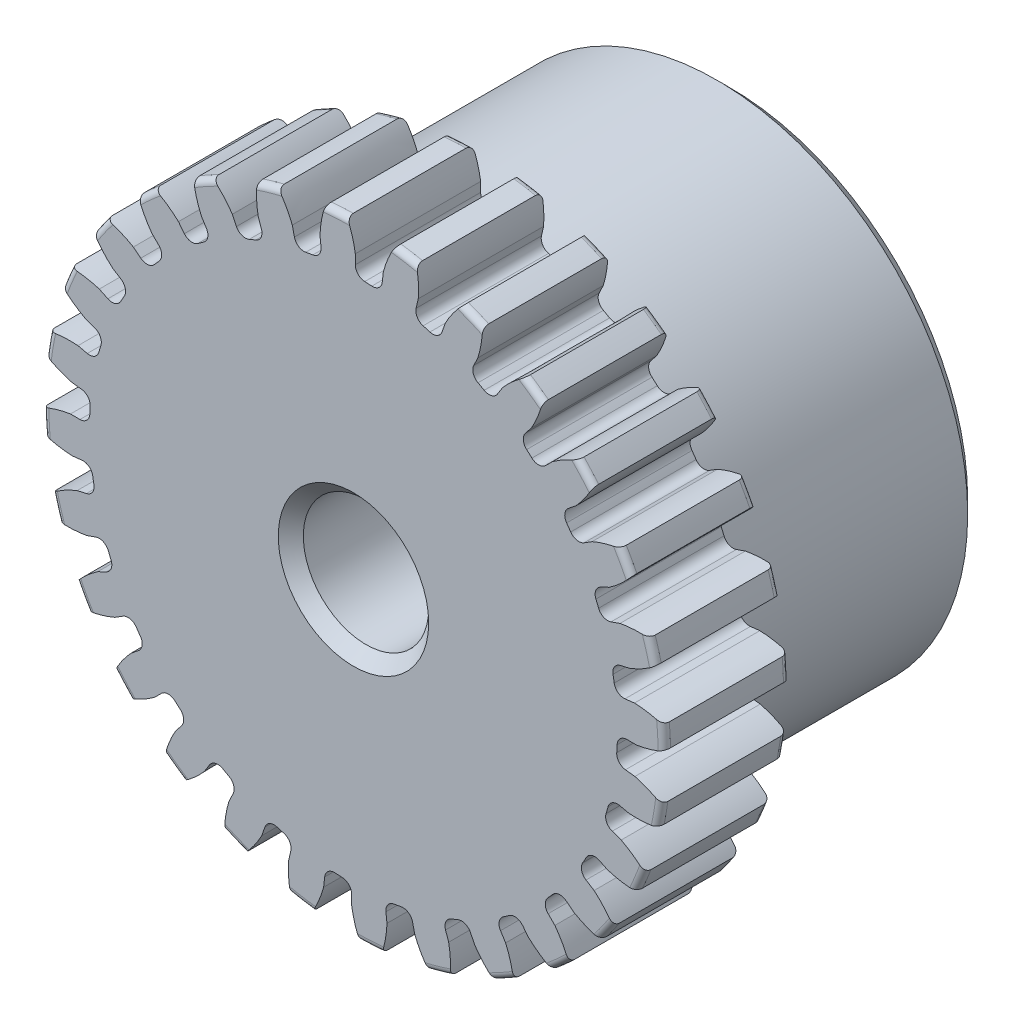
SolidWorks part; units mm, degrees
ref_plane "Front" through (0, 0, 0) normal (0, 0, 1) x (1, 0, 0)
ref_plane "Top" through (0, 0, 0) normal (0, 1, 0) x (1, 0, 0)
ref_plane "Right" through (0, 0, 0) normal (1, 0, 0) x (0, 0, -1)
sketch "Sketch1" plane through (0, 0, 0) normal (0, 0, 1) x (1, 0, 0)
  line L0 (-355.6, 0) -> (355.6, 0) construction
  circle A0 centre (0, 0) radius 7.874
  circle A1 centre (0, 0) radius 7.4041 construction
  circle A3 centre (0, 0) radius 6.6841 construction
  dimension "D1" = 1.1899
  dimension "OD" = 15.748
  dimension "Ptich Dia" = 14.8082
  dimension "Root Dia" = 13.3681
  dimension "D3" = 0.4699
  dimension "Number of Teeth" = 711.2
extrude "Boss-Extrude1" add sketch "Sketch1" against normal blind 3.175
sketch "Sketch2" plane through (0, 0, 0) normal (1, 0, 0) x (0, 0, -1)
  line L0 (3.175, 0) -> (9.525, 0)
  line L1 (3.175, 0) -> (3.175, 6.35)
  line L2 (3.175, 6.35) -> (9.525, 6.35)
  line L3 (9.525, 6.35) -> (9.525, 0)
  point P5 (9.525, -6.35)
  point P6 (0, -7.874)
  point P7 (3.175, -7.874)
  point P9 (0, 7.874)
  dimension "Face Wd" = 3.175
  dimension "B Hub Dia" = 12.7
  dimension "D O'all Lg." = 9.525
revolve "Revolve1" add sketch "Sketch2" angle 360 about L0
fillet "Fillet2" radius 0.1575 3 edges at (7.874, 0, -3.175) (7.874, 0, 0) (6.35, 0, -3.175)
sketch "Sketch3" plane through (0, 0, 0) normal (0, 0, 1) x (1, 0, 0)
  line L0 (0, 0) -> (0, 7.874) construction
  line L1 (-1.7948, 6.9399) -> (0, 7.4041)
  line L2 (-9.5921, 7.4041) -> (9.5921, 7.4041) construction
  line L3 (-9.2865, 5.0024) -> (9.2865, 9.8058) construction
  line L4 (-1.7948, 6.9399) -> (0, 0) construction
  line L5 (-4.5779, 5.516) -> (0, 0) construction
  line L6 (-4.5779, 5.516) -> (-0.7458, 8.6964) construction
  line L7 (-1.2515, 7.0582) -> (0, 0) construction
  line L8 (-1.2515, 7.0582) -> (0.0263, 7.2847) construction
  arc A0 (-1.7948, 6.9399) -> (-4.5779, 5.516) centre (0, 0) ccw
  circle A1 centre (0, 0) radius 7.4041 construction
  circle A2 centre (0, 0) radius 7.1683 construction
  arc A3 (-1.7948, 6.9399) -> (-1.2515, 7.0582) centre (0, 0) cw
  circle A4 centre (0, 0) radius 7.874 construction
  point P6 (0, 7.4041)
  dimension "D1" = 1.8538
  dimension "Pressure Angle" = 14.5
  dimension "D2" = 3.1515
  dimension "D3" = 4.98
  dimension "D4" = 0.5562
  dimension "D5" = 1.2977
sketch "Sketch4" plane through (0, 0, 0) normal (0, 0, 1) x (1, 0, 0)
  line L0 (0, 0) -> (0.4145, 7.3808) construction
  line L1 (0.0464, 7.1681) -> (0.0464, 6.6839)
  line L2 (0, 7.4041) -> (0.829, 7.3575) construction
  line L3 (0.7565, 7.1282) -> (0.7022, 6.6471)
  line L4 (0.0464, 6.6839) -> (0, 0) construction
  line L5 (0, 0) -> (0, 7.874) construction
  line L6 (-4.5779, 5.516) -> (-0.7458, 8.6964) construction
  line L7 (-4.5779, 5.516) -> (-0.7458, 8.6964) construction
  arc A0 (0.7022, 6.6471) -> (0.0464, 6.6839) centre (0, 0) ccw
  arc A1 (0, 7.4041) -> (0.829, 7.3575) centre (0, 0) cw construction
  circle A2 centre (0, 0) radius 7.4041 construction
  circle A3 centre (0, 0) radius 7.1683 construction
  circle A4 centre (0, 0) radius 6.6841 construction
  arc A5 (1.7148, 8.5582) -> (-0.7458, 8.6964) centre (0, 0) ccw
  spline S0 degree 2 poles (-0.7458, 8.6964) (-0.0823, 8.0256) (0.0464, 7.1681) knots 0 0 0 1 1 1
  spline S1 degree 2 poles (1.7148, 8.5582) (0.9804, 7.9659) (0.7565, 7.1282) knots 0 0 0 1 1 1
  dimension "D1" = 0.8307
extrude "Cut-Extrude1" cut sketch "Sketch4" against normal through all
fillet "Fillet1" radius 0.2492 2 edges at (0.7022, 6.6471, -1.5875) (0.0464, 6.6839, -1.5875)
pattern_circular "CirPattern1" count 28 over 360 about axis through (0, 0, -3.175) along (0, 0, 1) of "Cut-Extrude1", "Fillet1"
sketch "Sketch5" plane through (0, 0, 0) normal (0, 0, 1) x (1, 0, 0)
  circle A0 centre (0, 0) radius 1.5875
  circle A1 centre (0, 0) radius 1.5875 construction
  dimension "Bore Min" = 3.175
  dimension "Bore Max" = 3.175
extrude "Cut-Extrude2" cut sketch "Sketch5" against normal through all
chamfer "Chamfer1" distance 0.3175 angle 45 3 edges at (6.35, 0, -9.525) (1.5875, 0, 0) (1.5875, 0, -9.525)
sketch "Pitch Dia" plane through (0, 0, 0) normal (0, 0, 1) x (1, 0, 0)
  circle A0 centre (0, 0) radius 7.4041 construction
  circle A1 centre (0, 0) radius 7.4041 construction
equation "\"D1@Boss-Extrude1\" = \"Face Wd@Sketch2\""
equation "\"D2@Sketch3\" = \"D1@Sketch3\"*1.7"
equation "\"D3@Sketch3\" = \"D1@Sketch3\"+\"D2@Sketch3\"-.001"
equation "\"D4@Sketch3\" = \"D1@Sketch3\"*.3"
equation "\"D5@Sketch3\" = \"D1@Sketch3\"-\"D4@Sketch3\""
equation "\"D1@Sketch4\" = 1.5708/(\"Number of Teeth@Sketch1\"/\"Ptich Dia@Sketch1\")"
equation "\"D1@Chamfer1\" = \"B Hub Dia@Sketch2\"*.025"
equation "\"D1@CirPattern1\" = \"Number of Teeth@Sketch1\""
equation "\"D1@Fillet1\" = \"D1@Sketch4\"*.3"
equation "\"D1@Fillet2\" = \"OD@Sketch1\"*.01"
equation "\"D1@Sketch1\" = 2.250/(\"Number of Teeth@Sketch1\"/\"Ptich Dia@Sketch1\")"
